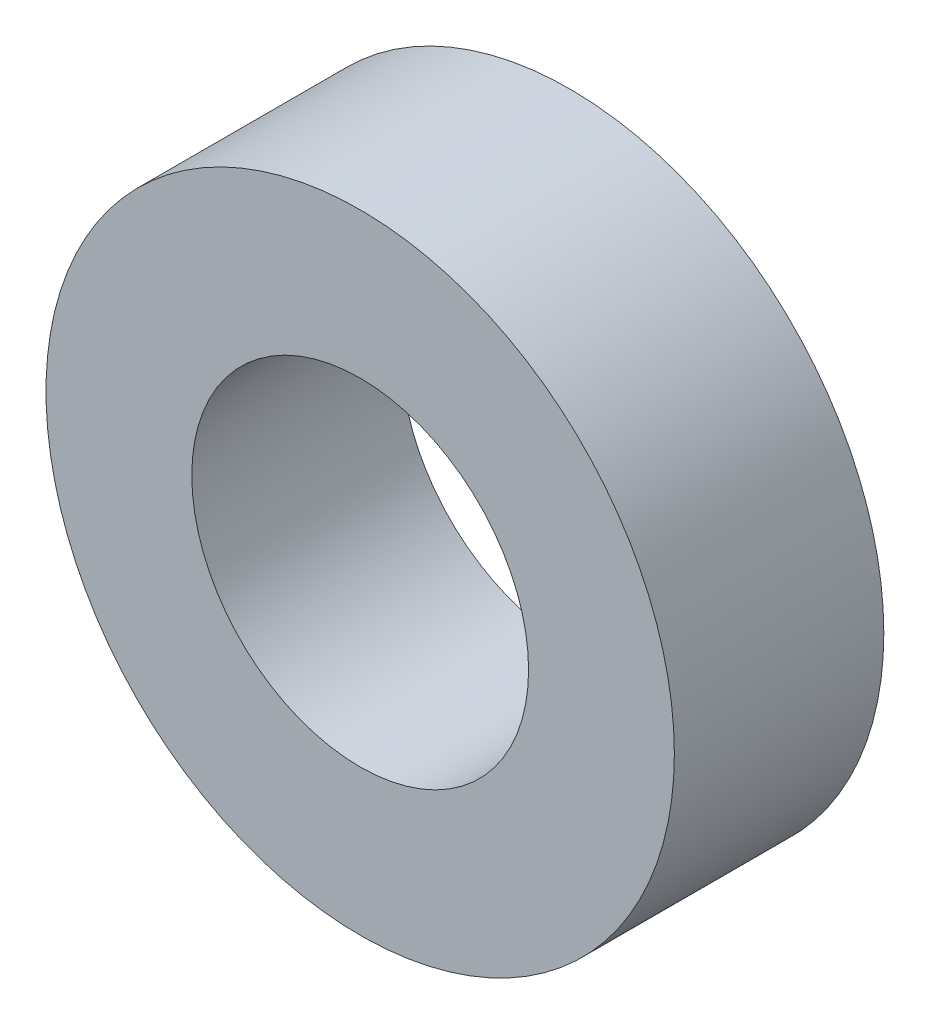
SolidWorks part; units mm, degrees
material "6061-T6 (SS)"
ref_plane "Front Plane" through (0, 0, 0) normal (0, 0, 1) x (1, 0, 0)
ref_plane "Top Plane" through (0, 0, 0) normal (0, 1, 0) x (1, 0, 0)
ref_plane "Right Plane" through (0, 0, 0) normal (1, 0, 0) x (0, 0, -1)
sketch "Sketch1" plane through (0, 0, 0) normal (0, 0, 1) x (1, 0, 0)
  circle A0 centre (0, 0) radius 2.5527
  circle A1 centre (0, 0) radius 4.7625
  dimension "D1" = 9.525
  dimension ".201" = 5.1054
extrude "Boss-Extrude1" add sketch "Sketch1" along normal blind 3.175
